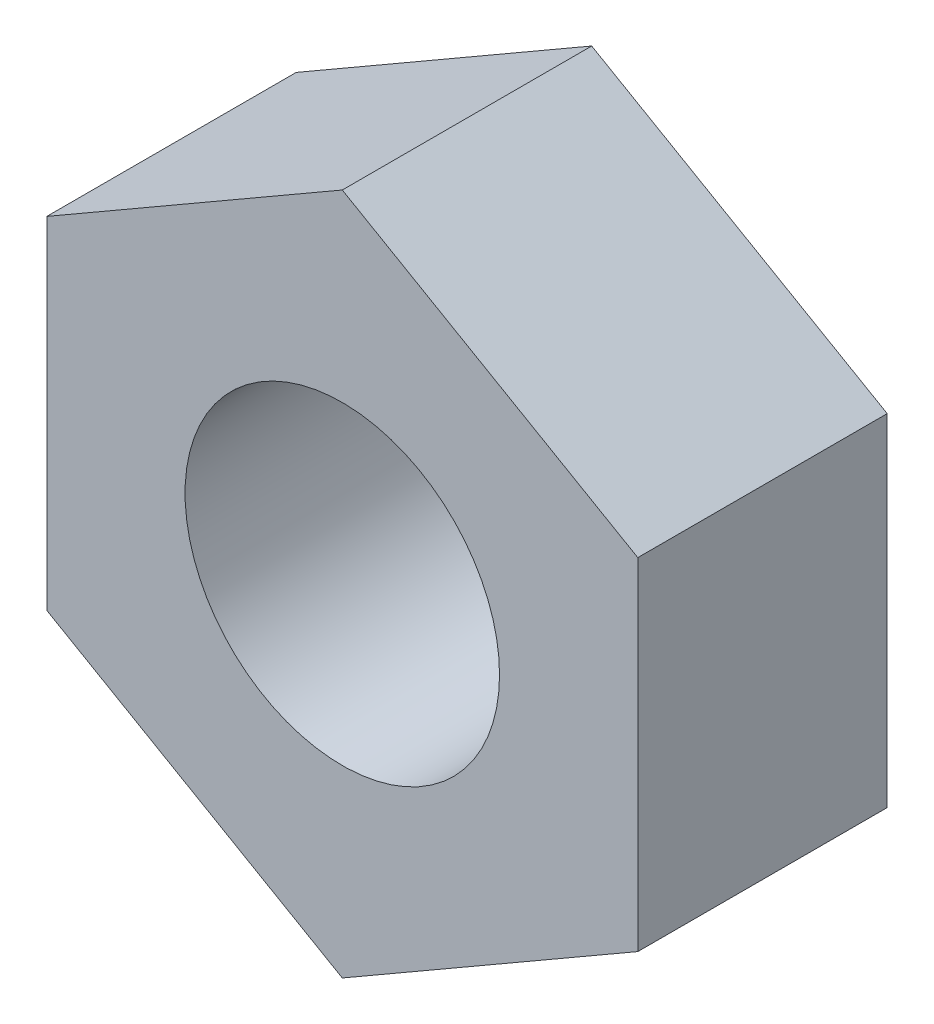
SolidWorks part; units mm, degrees
ref_plane "Plan de face" through (0, 0, 0) normal (0, 0, 1) x (1, 0, 0)
ref_plane "Plan de dessus" through (0, 0, 0) normal (0, 1, 0) x (1, 0, 0)
ref_plane "Plan de droite" through (0, 0, 0) normal (1, 0, 0) x (0, 0, -1)
sketch "Esquisse1" plane through (0, 0, 0) normal (0, 0, 1) x (1, 0, 0)
  line L1 (0, 3.1466) -> (-2.725, 1.5733)
  line L2 (-2.725, 1.5733) -> (-2.725, -1.5733)
  line L3 (-2.725, -1.5733) -> (0, -3.1466)
  line L4 (0, -3.1466) -> (2.725, -1.5733)
  line L5 (2.725, -1.5733) -> (2.725, 1.5733)
  line L6 (2.725, 1.5733) -> (0, 3.1466)
  circle A0 centre (0, 0) radius 2.725 construction
  circle A1 centre (0, 0) radius 1.45
extrude "Extrusion1" add sketch "Esquisse1" along normal blind 2.3
